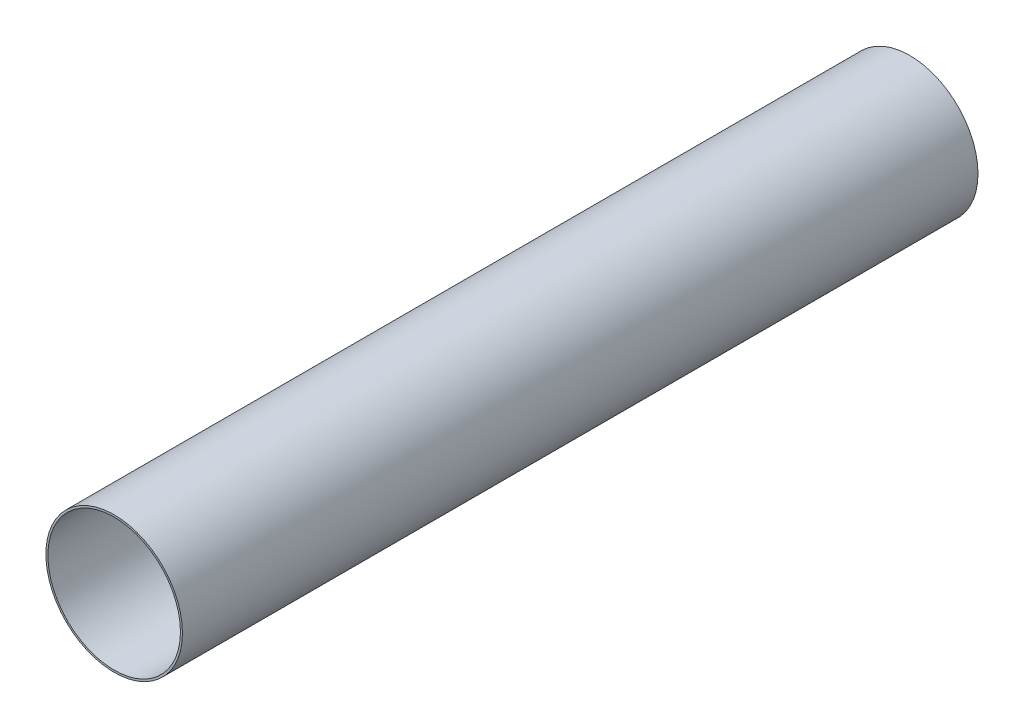
SolidWorks part; units mm, degrees
ref_plane "Front Plane" through (0, 0, 0) normal (0, 0, 1) x (1, 0, 0)
ref_plane "Top Plane" through (0, 0, 0) normal (0, 1, 0) x (1, 0, 0)
ref_plane "Right Plane" through (0, 0, 0) normal (1, 0, 0) x (0, 0, -1)
sketch "Sketch1" plane through (0, 0, 0) normal (0, 0, 1) x (1, 0, 0)
  circle A0 centre (0, 0) radius 65.405
  circle A1 centre (0, 0) radius 63.5
  dimension "D1" = 127
  dimension "D2" = 130.81
extrude "Boss-Extrude1" add sketch "Sketch1" along normal mid plane 762
equation "\"AIRFRAME_OD\"= 5.15in"
equation "\"AIRFRAME_ID\"= 5.00in"
equation "\"FLAT_T\"= 0.125in"
equation "\"NOSE_EXP_L\"= 27in"
equation "\"NOSE_SHOULDER_L\"= 5in"
equation "\"MAIN_L\"= 30in"
equation "\"RECO_COUP_L\"= 10in"
equation "\"RECO_SWITCH_L\"= 2in"
equation "\"DROGUE_L\"= 20in"
equation "\"ATS_FORE_COUP_L\"= 5.5in"
equation "\"ATS_AFT_COUP_L\"= 4.5in"
equation "\"LOWER_L\"= 30in"
equation "\"FIN_N\"= 4"
equation "\"CR_AFT_X\"= 0.5in"
equation "\"CR_FORE_X\"= 9.25in"
equation "\"D1@Sketch1\"=\"AIRFRAME_ID\""
equation "\"D2@Sketch1\"=\"AIRFRAME_OD\""
equation "\"D1@Boss-Extrude1\"=\"MAIN_L\""
equation "\"FIN_ROOT\"= 8in"
equation "\"FIN_X\"= 0.75in"
equation "\"MOTOR_OD\"= 3.091in"
equation "\"MOTOR_ID\"= 3.00in"
equation "\"COUPLER_OD\"= 4.998in"
equation "\"COUPLER_ID\"= 4.88in"
equation "\"RECO_ROD_X\"= 3.5in"
equation "\"ATS_ROD_X\"= 3.75in"
equation "\"MOTOR_L\"= 14in"
equation "\"MOTOR_LOWER_X\"= 2in"
